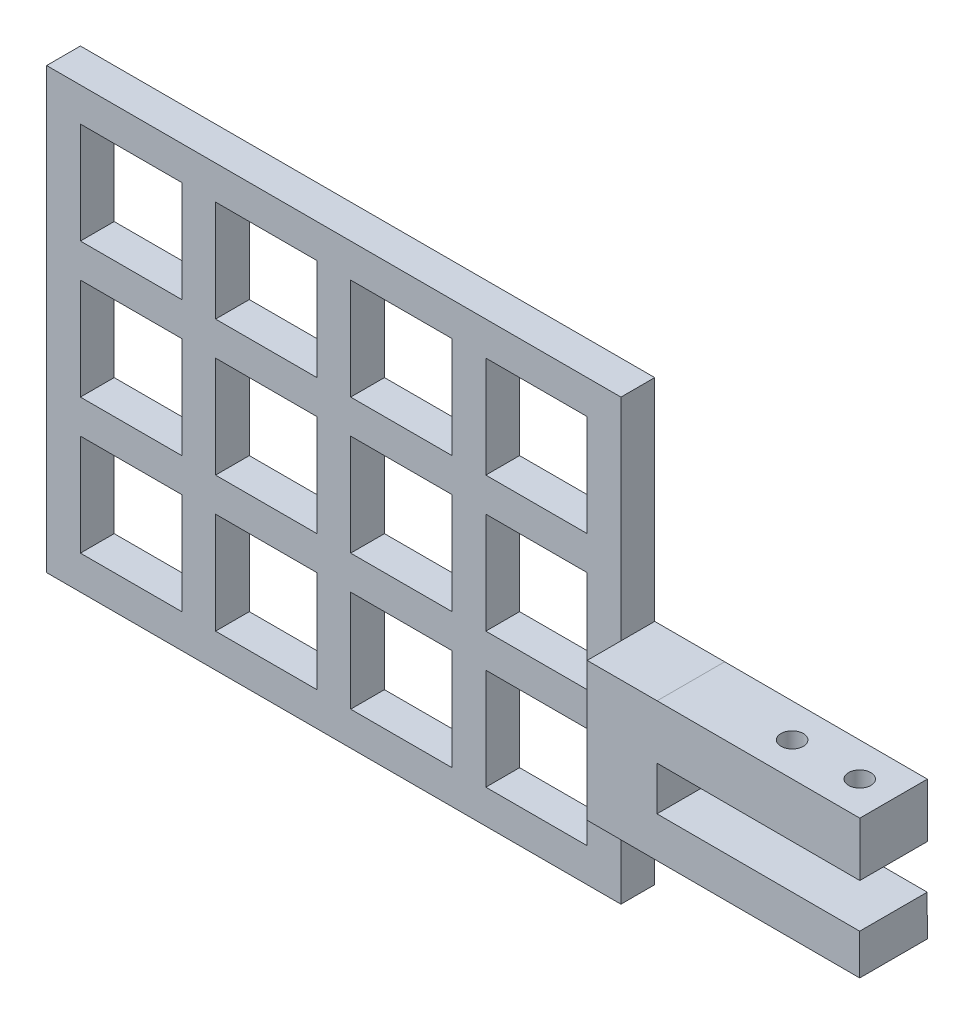
SolidWorks part; units mm, degrees
ref_plane "前视基准面" through (0, 0, 0) normal (0, 0, 1) x (1, 0, 0)
ref_plane "上视基准面" through (0, 0, 0) normal (0, 1, 0) x (1, 0, 0)
ref_plane "右视基准面" through (0, 0, 0) normal (1, 0, 0) x (0, 0, -1)
other "Configuration Table"
sketch "草图1" plane through (0, 0, 0) normal (0, 0, 1) x (1, 0, 0)
  line L0 (0.0201, -0.0524) -> (0.0169, 5.9476)
  line L1 (0.0169, 5.9476) -> (-29.9831, 5.9866)
  line L2 (-29.9831, 5.9866) -> (-29.9624, 12.4866)
  line L3 (-29.9624, 12.4866) -> (0.0376, 12.4476)
  line L4 (0.0376, 12.4476) -> (0.0376, 20.4476)
  line L5 (0.0376, 20.4476) -> (-29.9624, 20.4866)
  line L9 (-40.3152, 20.4866) -> (-40.3152, 0)
  line L10 (-40.3152, 0) -> (0.0201, -0.0524)
  line L16 (-29.9624, 20.4866) -> (-40.3152, 20.4866)
  dimension "D1" = 8
  dimension "D2" = 6
  dimension "D3" = 6.5
  dimension "D6" = 30
  dimension "D7" = 30
extrude "凸台-拉伸1" add sketch "草图1" along normal blind 10
sketch "草图2" plane through (0.0265, 20.4476, 0) normal (0.0013, 1, 0) x (1, -0.0013, 0)
  line L0 (0.0111, -10) -> (-29.9889, -10) construction
  line L1 (0, 0) -> (-10, 0) construction
  line L2 (0, 0) -> (0, -10) construction
  line L3 (0, -10) -> (-10, -10) construction
  line L4 (-10, 0) -> (-10, -10) construction
  line L5 (0, 0) -> (-10, -10) construction
  line L6 (0, -10) -> (-10, 0) construction
  line L8 (-10, 0) -> (-20, 0) construction
  line L9 (-10, 0) -> (-10, -10) construction
  line L10 (-10, -10) -> (-20, -10) construction
  line L11 (-20, 0) -> (-20, -10) construction
  line L12 (-10, 0) -> (-20, -10) construction
  line L13 (-10, -10) -> (-20, 0) construction
  point P4 (-5, -5)
  point P10 (-15, -5)
  dimension "D1" = 10
  dimension "D2" = 10
hole_wizard "M4 螺纹孔的螺纹孔钻头1" positions "草图3" profile "草图4" hole size "M4" standard "ISO" end condition up to next
sketch "草图3" plane through (0.0265, 20.4476, 0) normal (0.0013, 1, 0) x (1, -0.0013, 0)
  point P0 (-15, -5)
  point P3 (-5, -5)
sketch "草图4" plane through (-14.9734, 20.4671, 5) normal (0, 0, 1) x (-1, 0.0013, 0)
  line L0 (0, 0) -> (0, 8)
  line L1 (0, 8) -> (1.65, 8)
  line L2 (1.65, 8) -> (1.65, 0)
  line L5 (1.65, 0) -> (0, 0)
  line L11 (0, -6.35) -> (0, 107.95) construction
  dimension "通孔孔直径" = 3.3
  dimension "通孔孔深度" = 8
sketch "草图5" plane through (0.0162, 12.4476, 0) normal (-0.0013, -1, 0) x (1, -0.0013, 0)
  line L0 (-10, 0) -> (-20, 10) construction
  line L1 (0, 0) -> (-10, 10) construction
  line L3 (-16.077, 2.2) -> (-13.923, 2.2)
  line L5 (-16.077, 7.8) -> (-13.923, 7.8)
  line L7 (-16.077, 2.2) -> (-13.923, 7.8) construction
  line L8 (-16.077, 7.8) -> (-13.923, 2.2) construction
  line L9 (-6.077, 2.2) -> (-3.923, 2.2)
  line L11 (-6.077, 7.8) -> (-3.923, 7.8)
  line L13 (-6.077, 2.2) -> (-3.923, 7.8) construction
  line L14 (-6.077, 7.8) -> (-3.923, 2.2) construction
  arc A0 (-16.077, 7.8) -> (-16.077, 2.2) centre (-15, 5) ccw
  arc A1 (-6.077, 7.8) -> (-6.077, 2.2) centre (-5, 5) ccw
  arc A2 (-13.923, 2.2) -> (-13.923, 7.8) centre (-15, 5) ccw
  arc A3 (-3.923, 2.2) -> (-3.923, 7.8) centre (-5, 5) ccw
  dimension "D1" = 6
  dimension "D2" = 6
  dimension "D3" = 5.6
  dimension "D4" = 5.6
extrude "切除-拉伸1" cut sketch "草图5" against normal blind 5
sketch "草图6" plane through (0, 0, 0) normal (0, 0, 1) x (1, 0, 0)
  line L0 (-40.3152, -13.2634) -> (-40.3152, 51.7366) construction
  line L1 (-40.3152, 51.7366) -> (-40.3152, 9.2366) construction
  line L3 (-40.3152, 51.7366) -> (-125.3152, 51.7366)
  line L4 (-40.3152, 51.7366) -> (-40.3152, -13.2634)
  line L5 (-40.3152, -13.2634) -> (-125.3152, -13.2634)
  line L6 (-125.3152, 51.7366) -> (-125.3152, -13.2634)
  line L7 (-40.3152, 51.7366) -> (-125.3152, -13.2634) construction
  line L8 (-40.3152, -13.2634) -> (-125.3152, 51.7366) construction
  line L9 (-29.9727, 9.2366) -> (-40.3152, 9.2366) construction
  line L12 (-29.9831, 5.9866) -> (-29.9624, 12.4866) construction
  point P3 (-40.3152, 8.6072)
  point P5 (-82.8152, 19.2366)
  dimension "D1" = 65
  dimension "D2" = 85
  dimension "D4" = 42.5
extrude "凸台-拉伸2" add sketch "草图6" along normal blind 5
sketch "草图7" plane through (0, 0, 5) normal (0, 0, 1) x (1, 0, 0)
  line L1 (-125.3152, 51.7366) -> (-120.3152, 51.7366) construction
  line L2 (-125.3152, 51.7366) -> (-125.3152, 46.7366) construction
  line L3 (-125.3152, 46.7366) -> (-120.3152, 46.7366) construction
  line L4 (-120.3152, 51.7366) -> (-120.3152, 46.7366) construction
  line L5 (-125.3152, 51.7366) -> (-120.3152, 46.7366) construction
  line L6 (-125.3152, 46.7366) -> (-120.3152, 51.7366) construction
  line L7 (-120.3152, 46.7366) -> (-105.3152, 46.7366)
  line L8 (-120.3152, 46.7366) -> (-120.3152, 31.7366)
  line L9 (-120.3152, 31.7366) -> (-105.3152, 31.7366)
  line L10 (-105.3152, 46.7366) -> (-105.3152, 31.7366)
  line L11 (-120.3152, 46.7366) -> (-105.3152, 31.7366) construction
  line L12 (-120.3152, 31.7366) -> (-105.3152, 46.7366) construction
  point P4 (-122.8152, 49.2366)
  point P9 (-112.8152, 39.2366)
  dimension "D1" = 5
  dimension "D2" = 5
  dimension "D3" = 15
  dimension "D4" = 15
extrude "切除-拉伸2" cut sketch "草图7" against normal blind 5
pattern_linear "阵列(线性)1" count 4 spacing 20 along (1, 0, 0) count 3 spacing 20 along (0, -1, 0) of "切除-拉伸2"
